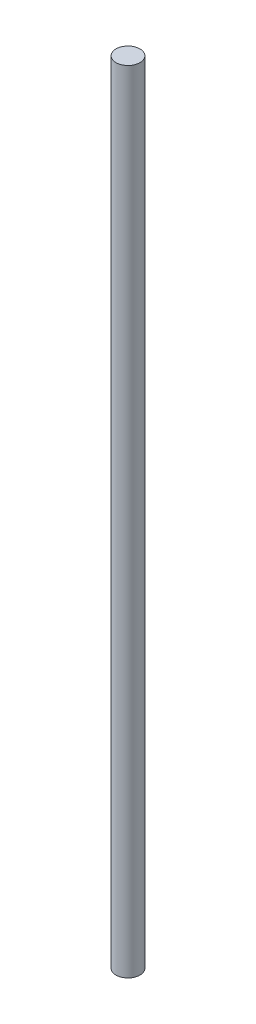
SolidWorks part; units mm, degrees
ref_plane "Alzado" through (0, 0, 0) normal (0, 0, 1) x (1, 0, 0)
ref_plane "Planta" through (0, 0, 0) normal (0, 1, 0) x (1, 0, 0)
ref_plane "Vista lateral" through (0, 0, 0) normal (1, 0, 0) x (0, 0, -1)
sketch "Croquis1" plane through (0, 0, 0) normal (0, 1, 0) x (1, 0, 0)
  circle A0 centre (0, 0) radius 6.35
  dimension "D1" = 12.7
sketch "Croquis2" plane through (0, 0, 0) normal (0, 0, 1) x (1, 0, 0)
  line L0 (0, 0) -> (0, 420)
  dimension "D1" = 420
sweep "Barrer1" add profiles "Croquis1" path "Croquis2"
